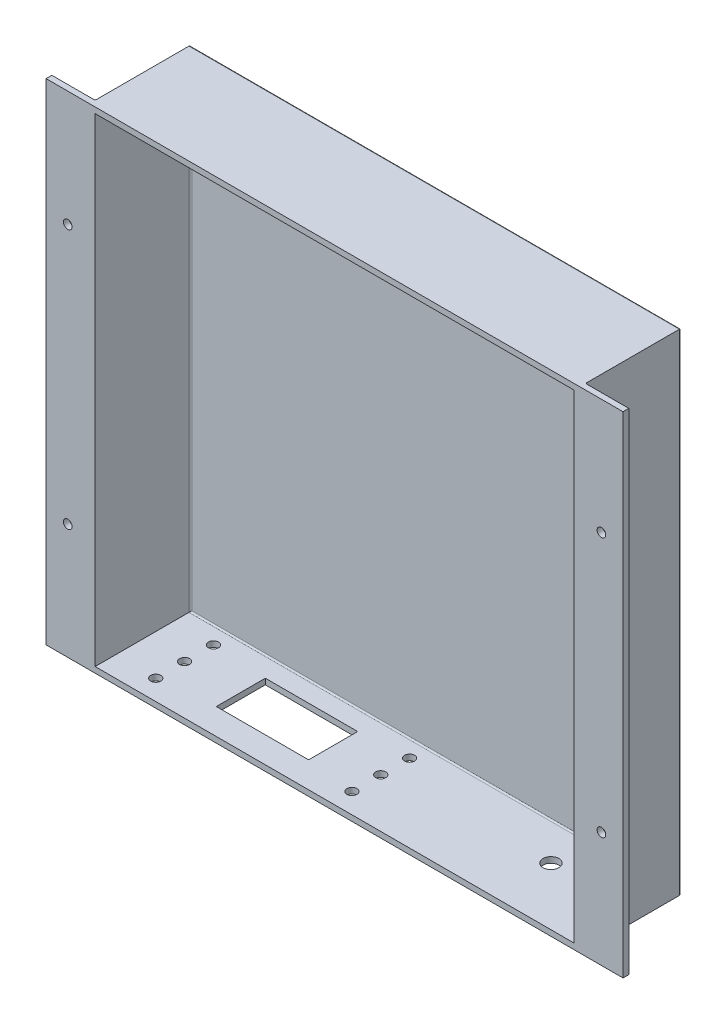
SolidWorks part; units mm, degrees
ref_plane "Front Plane" through (0, 0, 0) normal (0, 0, 1) x (1, 0, 0)
ref_plane "Top Plane" through (0, 0, 0) normal (0, 1, 0) x (1, 0, 0)
ref_plane "Right Plane" through (0, 0, 0) normal (1, 0, 0) x (0, 0, -1)
sketch "Sketch1" plane through (0, 0, 0) normal (0, 0, 1) x (1, 0, 0)
  line L1 (-85, -85) -> (85, -85)
  line L2 (-85, -85) -> (-85, 85)
  line L3 (-85, 85) -> (85, 85)
  line L4 (85, -85) -> (85, 85)
  line L5 (-85, -85) -> (85, 85) construction
  line L6 (-85, 85) -> (85, -85) construction
  point P0 (0, 0)
  dimension "D1" = 170
  dimension "D2" = 170
extrude "Boss-Extrude1" add sketch "Sketch1" along normal blind 35
sketch "Sketch2" plane through (0, 0, 35) normal (0, 0, 1) x (1, 0, 0)
  line L1 (83, 83) -> (-83, 83)
  line L2 (83, 83) -> (83, -83)
  line L3 (83, -83) -> (-83, -83)
  line L4 (-83, 83) -> (-83, -83)
  line L5 (85, 85) -> (-85, 85) construction
  line L6 (-85, -85) -> (85, -85) construction
  line L7 (-85, 85) -> (-85, -85) construction
  line L8 (85, -85) -> (85, 85) construction
  dimension "D1" = 2
  dimension "D2" = 2
  dimension "D3" = 2
  dimension "D4" = 2
extrude "Cut-Extrude1" cut sketch "Sketch2" against normal blind 33
sketch "Sketch3" plane through (85, 0, 0) normal (1, 0, 0) x (0, 0, -1)
  line L0 (-35, -85) -> (0, -85) construction
  line L1 (-35, 85) -> (-33, 85)
  line L2 (-35, 85) -> (-35, -85)
  line L3 (-35, -85) -> (-33, -85)
  line L4 (-33, 85) -> (-33, -85)
  dimension "D1" = 2
extrude "Boss-Extrude2" add sketch "Sketch3" along normal blind 15
sketch "Sketch4" plane through (-85, 0, 0) normal (-1, 0, 0) x (0, 0, 1)
  line L0 (35, -85) -> (0, -85) construction
  line L1 (35, 85) -> (33, 85)
  line L2 (35, 85) -> (35, -85)
  line L3 (35, -85) -> (33, -85)
  line L4 (33, 85) -> (33, -85)
  dimension "D1" = 2
extrude "Boss-Extrude3" add sketch "Sketch4" along normal blind 15
hole_wizard "Ø3.0 (3) Diameter Hole1" positions "Sketch6" profile "Sketch5" hole size "Ø3.0" standard "Ansi Metric"
sketch "Sketch6" plane through (0, 0, 35) normal (0, 0, 1) x (1, 0, 0)
  line L0 (100, 85) -> (-100, 85) construction
  line L1 (-100, -85) -> (-100, 85) construction
  line L2 (-100, -85) -> (100, -85) construction
  line L3 (100, 85) -> (100, -85) construction
  point P0 (-92.5, 45)
  point P12 (-92.5, -45)
  point P16 (115, -45) [skipped]
  point P17 (115, 45) [skipped]
  point P21 (92.5, 45)
  point P22 (92.5, -45)
  dimension "D1" = 40
  dimension "D4" = 7.5
  dimension "D6" = 0
  dimension "D7" = 40
  dimension "D8" = 40
  dimension "D9" = 40
  dimension "D10" = 7.5
  dimension "D2" = 2
  dimension "D3" = 2
  dimension "D5" = 2
sketch "Sketch5" plane through (-92.5, 45, 35) normal (1, 0, 0) x (0, -1, 0)
  line L0 (0, 0) -> (0, 100.9013)
  line L1 (0, 100.9013) -> (1.5, 100)
  line L2 (1.5, 100) -> (1.5, 0)
  line L5 (1.5, 0) -> (0, 0)
  line L10 (0, 100.9013) -> (-1.5, 100) construction
  line L11 (0, -6.35) -> (0, 107.95) construction
  dimension "Hole Dia." = 3
  dimension "Hole Depth" = 100
  dimension "Drill Angle" = 118
sketch "Sketch7" plane through (0, -85, 0) normal (0, -1, 0) x (1, 0, 0)
  line L1 (-50, 26) -> (-18, 26)
  line L2 (-50, 26) -> (-50, 9)
  line L3 (-50, 9) -> (-18, 9)
  line L4 (-18, 26) -> (-18, 9)
  line L5 (-85, 0) -> (85, 0) construction
  line L6 (-85, 33) -> (-85, 0) construction
  line L7 (-100, 35) -> (100, 35) construction
  line L12 (85, 33) -> (85, 0) construction
  circle A0 centre (55, 15) radius 2.75
  circle A1 centre (70, 15) radius 2.75
  dimension "D6" = 5.5
  dimension "D1" = 15
  dimension "D2" = 32
  dimension "D3" = 17
  dimension "D4" = 9
  dimension "D7" = 30
  dimension "D8" = 15
  dimension "D5" = 35
  dimension "D9" = 9
extrude "Cut-Extrude2" cut sketch "Sketch7" against normal blind 15
fillet "Fillet1" radius 0.5 9 edges at (-83, 0, 2) (83, 0, 2) (85, 0, 0) (-85, 0, 0) (0, -85, 0) (0, 85, 0) (0, -83, 2)
hole_wizard "Ø3.5 (3.5) Diameter Hole1" positions "Sketch9" profile "Sketch8" hole size "Ø3.5" standard "Ansi Metric"
sketch "Sketch9" plane through (0, -85, 0) normal (0, -1, 0) x (1, 0, 0)
  line L0 (-50, 26) -> (-50, 9) construction
  line L2 (-18, 26) -> (-50, 26) construction
  point P0 (-69, 28)
  point P19 (-1, 28)
  point P20 (-69, 18)
  point P21 (-1, 18)
  point P22 (-69, 8)
  point P23 (-1, 8)
  dimension "D1" = 19
  dimension "D2" = 2
  dimension "D4" = 2
  dimension "D3" = 3
sketch "Sketch8" plane through (-69, -85, 28) normal (1, 0, 0) x (0, 0, -1)
  line L0 (0, 0) -> (0, 101.0515)
  line L1 (0, 101.0515) -> (1.75, 100)
  line L2 (1.75, 100) -> (1.75, 0)
  line L5 (1.75, 0) -> (0, 0)
  line L10 (0, 101.0515) -> (-1.75, 100) construction
  line L11 (0, -6.35) -> (0, 107.95) construction
  dimension "Hole Dia." = 3.5
  dimension "Hole Depth" = 100
  dimension "Drill Angle" = 118
